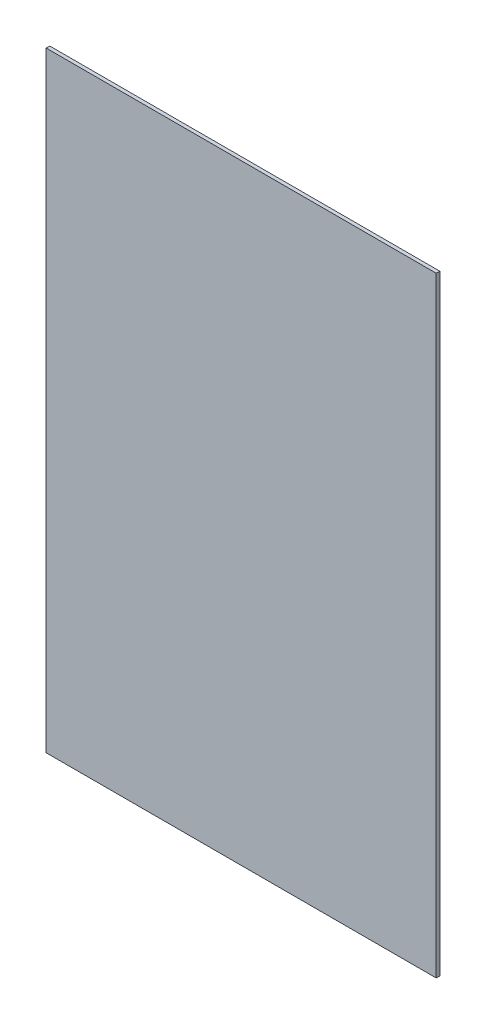
SolidWorks part; units mm, degrees
material "PC High Viscosity"
ref_plane "Front Plane" through (0, 0, 0) normal (0, 0, 1) x (1, 0, 0)
ref_plane "Top Plane" through (0, 0, 0) normal (0, 1, 0) x (1, 0, 0)
ref_plane "Right Plane" through (0, 0, 0) normal (1, 0, 0) x (0, 0, -1)
sketch "Sketch1" plane through (0, 0, 0) normal (0, 0, 1) x (1, 0, 0)
  line L0 (-12781.0305, 9771.1484) -> (-10081.0305, 9771.1484) construction
  line L1 (-11493.7606, 8062.1398) -> (-12585.8718, 8062.1398)
  line L2 (-11493.7606, 8062.1398) -> (-11493.7606, 9771.1484)
  line L3 (-11493.7606, 9771.1484) -> (-12585.8718, 9771.1484)
  line L4 (-12585.8718, 8062.1398) -> (-12585.8718, 9771.1484)
  line L5 (-12781.0305, 8062.1398) -> (-10081.0305, 8062.1398) construction
extrude "Boss-Extrude1" add sketch "Sketch1" along normal blind 10
